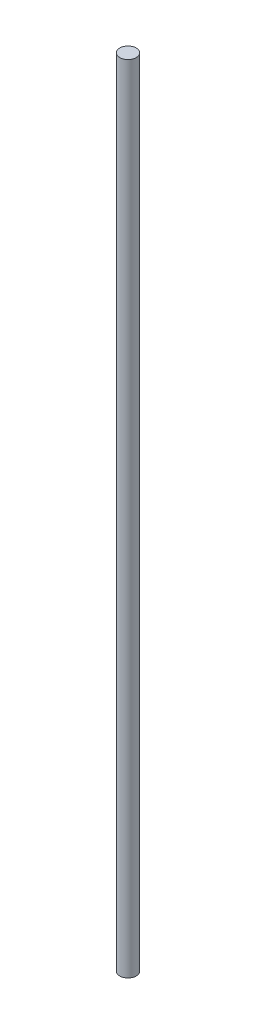
SolidWorks part; units mm, degrees
ref_plane "Front Plane" through (0, 0, 0) normal (0, 0, 1) x (1, 0, 0)
ref_plane "Top Plane" through (0, 0, 0) normal (0, 1, 0) x (1, 0, 0)
ref_plane "Right Plane" through (0, 0, 0) normal (1, 0, 0) x (0, 0, -1)
sketch "Sketch1" plane through (0, 0, 0) normal (0, 1, 0) x (1, 0, 0)
  circle A0 centre (0, 0) radius 3.175
  dimension "D1" = 6.35
extrude "Boss-Extrude1" add sketch "Sketch1" along normal blind 304.8
